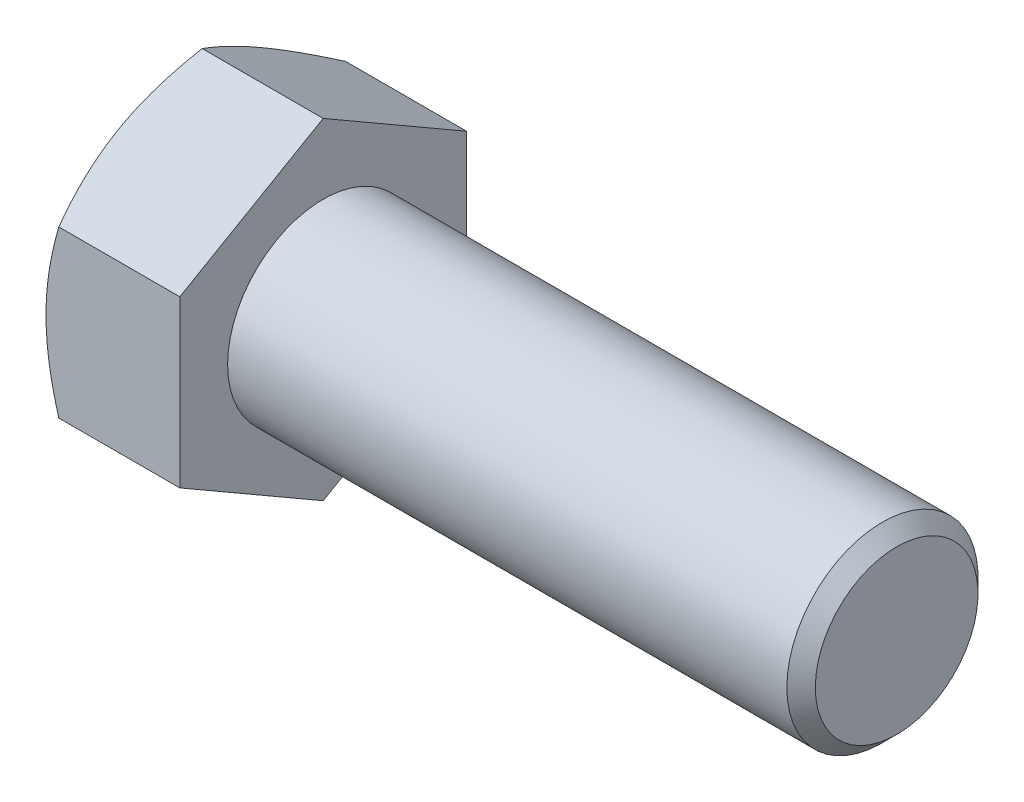
SolidWorks part; units mm, degrees
extrude "BaseHead" add sketch "Sketch1" along normal blind 17.78
sketch "Sketch1" plane through (0, 0, 0) normal (1, 0, 0) x (0, 0, -1)
  line L0 (19.05, 10.9985) -> (19.05, -10.9985)
  line L1 (-19.05, 10.9985) -> (-19.05, -10.9985)
  line L2 (19.05, -10.9985) -> (0, -21.997)
  line L3 (0, -21.997) -> (-19.05, -10.9985)
  line L4 (19.05, 10.9985) -> (0, 21.997)
  line L5 (0, 21.997) -> (-19.05, 10.9985)
  dimension "D2" = 120
ref_plane "Plane1" through (0, 0, 0) normal (0, 0, 1) x (1, 0, 0)
ref_plane "Plane2" through (0, 0, 0) normal (0, 1, 0) x (1, 0, 0)
ref_plane "Plane3" through (0, 0, 0) normal (1, 0, 0) x (0, 0, -1)
sketch "BodySke" plane through (0, 0, 0) normal (0, 0, 1) x (1, 0, 0)
  line L0 (0, 10.9985) -> (0, -10.9985) construction
  line L1 (0, 0) -> (93.98, 0)
  line L2 (0, 0) -> (0, 12.7)
  line L3 (0, 12.7) -> (92.0877, 12.7)
  line L4 (93.98, 0) -> (93.98, 10.8077)
  line L5 (17.78, 21.997) -> (17.78, 10.9985) construction
  line L6 (93.98, 10.8077) -> (92.0877, 12.7)
  line L7 (0, 0) -> (96.52, 0) construction
  line L8 (93.98, -10.8077) -> (92.0877, -12.7) construction
  line L9 (0, -12.7) -> (92.0877, -12.7) construction
  line L10 (19.8882, 15.24) -> (19.8882, -2.54) construction
  line L11 (62.23, 15.24) -> (62.23, -2.54) construction
  line L12 (17.78, 10.9985) -> (17.78, -10.9985) construction
revolve "BaseBody" add sketch "BodySke" angle 360 about L7
cosmetic thread "ThreadCosmetic" [suppressed] parameters "Thread_length"=31.75, "Thread_minor"=21.6154
sketch "Sketch3" plane through (0, 0, 0) normal (0, 0, 1) x (1, 0, 0)
  line L0 (0, 19.05) -> (5.3677, 28.347)
  line L1 (0, 21.997) -> (0, 10.9985) construction
  line L2 (5.3677, 28.347) -> (5.3677, 34.697)
  line L3 (5.3677, 34.697) -> (-12.7, 34.697)
  line L4 (-12.7, 34.697) -> (-12.7, 19.05)
  line L5 (-12.7, 19.05) -> (0, 19.05)
  line L6 (0, 0) -> (99.06, 0) construction
  line L7 (17.78, 21.997) -> (0, 21.997) construction
  dimension "D2" = 6.35
  dimension "D3" = 12.7
  dimension "D4" = 6.35
  dimension "Head_ch_ang" = 30
revolve "HeadChamfer" cut sketch "Sketch3" angle 360 about L6
fillet "HeadFillet" [suppressed] radius 2.286
sketch "ThdSchSke" plane through (0, 0, 0) normal (0, 0, 1) x (1, 0, 0)
  line L0 (62.23, -10.8077) -> (60.905, -12.7)
  line L1 (62.23, -10.8077) -> (63.555, -12.7)
  line L2 (63.555, -12.7) -> (63.555, -15.875)
  line L3 (-3.175, 0) -> (5.1513, 0) construction
  line L5 (63.555, -15.875) -> (60.905, -15.875)
  line L6 (60.905, -15.875) -> (60.905, -12.7)
revolve "ThreadSchematic" [suppressed] cut sketch "ThdSchSke" angle 360 about L3
pattern_linear "ThdSchPat" [suppressed]
equation "\"D3@Sketch1\" = \"Width_flats@Sketch1\" / 2"
equation "\"D4@Sketch1\" = \"D3@Sketch1\""
equation "\"D5@Sketch1\" = \"D4@Sketch1\""
equation "\"Thread_minor@ThreadCosmetic\" = \"Minor_dia@BodySke\""
equation "\"D1@Sketch3\" = \"Width_flats@Sketch1\" / 2"
equation "\"Thread_length@ThreadCosmetic\" = ((sgn( (\"Length@BodySke\" - \"Advance@BodySke\" ) - \"Thread_nom@BodySke\" )-1)*( (\"Length@BodySke\" - \"Advance@BodySke\" ) - \"Thread_nom@BodySke\" ))/-2+ \"Thread_nom@BodySke\""
equation "\"Thread_minor@ThdSchSke\" = \"Minor_dia@BodySke\""
equation "\"Diameter@ThdSchSke\" = \"Diameter@BodySke\""
equation "\"Overcut@ThdSchSke\" = \"Diameter@BodySke\" * 1.25"
equation "\"Start@ThdSchSke\" = \"Head_ht@BaseHead\" + \"Length@BodySke\" - \"Thread_length@ThreadCosmetic\"  '---Non-countersunk---"
equation "\"Num_threads@ThdSchPat\" = int( \"Thread_length@ThreadCosmetic\" / \"Advance@BodySke\" + 0.999 )  + 1"
equation "\"Advance@ThdSchPat\" = \"Thread_length@ThreadCosmetic\" /  (\"Num_threads@ThdSchPat\" - 1) 'relax it"
equation "\"Num_threads@ThdSchPat\" = \"Num_threads@ThdSchPat\" - sgn( \"Num_threads@ThdSchPat\" - 1) '---chamfered tips only---"
